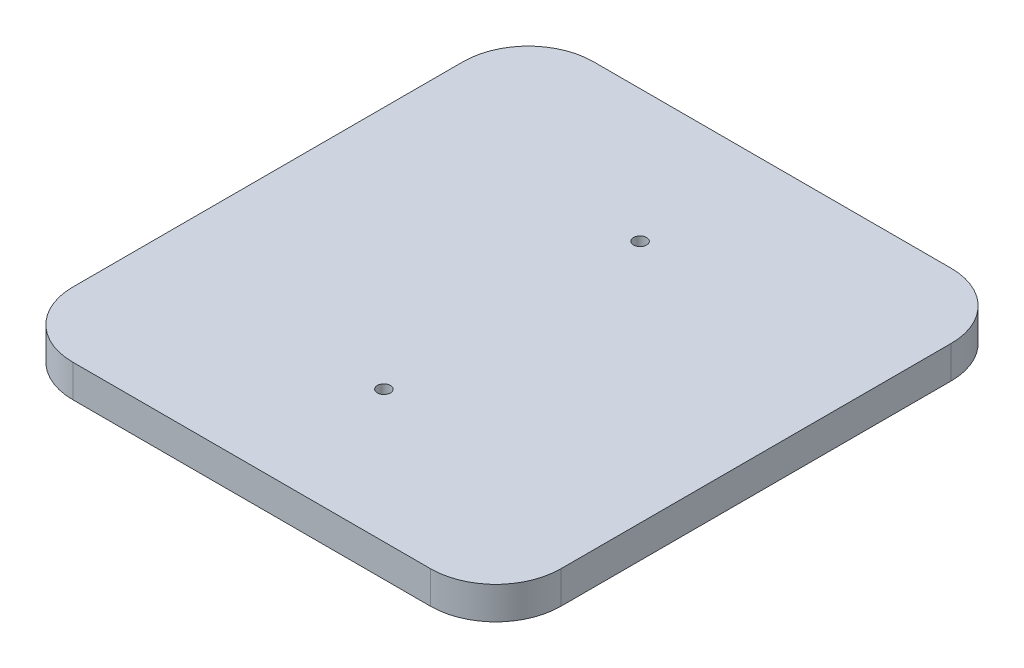
SolidWorks part; units mm, degrees
ref_plane "Front Plane" through (0, 0, 0) normal (0, 0, 1) x (1, 0, 0)
ref_plane "Top Plane" through (0, 0, 0) normal (0, 1, 0) x (1, 0, 0)
ref_plane "Right Plane" through (0, 0, 0) normal (1, 0, 0) x (0, 0, -1)
sketch "Sketch1" plane through (0, 0, 0) normal (0, 1, 0) x (1, 0, 0)
  line L1 (25.4, 0) -> (165.1, 0)
  line L2 (0, 25.4) -> (0, 177.8)
  line L3 (25.4, 203.2) -> (165.1, 203.2)
  line L4 (190.5, 25.4) -> (190.5, 177.8)
  arc A0 (0, 25.4) -> (25.4, 0) centre (25.4, 25.4) ccw
  arc A1 (165.1, 0) -> (190.5, 25.4) centre (165.1, 25.4) ccw
  arc A2 (190.5, 177.8) -> (165.1, 203.2) centre (165.1, 177.8) ccw
  arc A3 (25.4, 203.2) -> (0, 177.8) centre (25.4, 177.8) ccw
  point P7 (0, 0)
  dimension "D1" = 25.4
extrude "Boss-Extrude1" add sketch "Sketch1" along normal blind 12.7
hole_wizard "1/4-20 Tapped Hole2" positions "Sketch5" profile "Sketch4" tap size "1/4-20" standard "ANSI Inch"
sketch "Sketch5" plane through (0, 12.7, 0) normal (0, 1, 0) x (1, 0, 0)
  line L0 (25.4, 0) -> (165.1, 0) construction
  line L1 (0, 177.8) -> (0, 25.4) construction
  point P0 (95.25, 151.6)
  point P2 (95.25, 51.6)
  dimension "D1" = 100
  dimension "D2" = 51.6
  dimension "D3" = 95.25
sketch "Sketch4" plane through (95.25, 12.7, -151.6) normal (1, 0, 0) x (0, 0, 1)
  line L0 (0, 0) -> (0, 20.5838)
  line L1 (0, 20.5838) -> (2.5527, 19.05)
  line L2 (2.5527, 19.05) -> (2.5527, 0)
  line L5 (2.5527, 0) -> (0, 0)
  line L10 (0, 20.5838) -> (-2.5527, 19.05) construction
  line L11 (0, -6.35) -> (0, 107.95) construction
  dimension "Tap Drill Dia." = 5.1054
  dimension "Tap Drill Depth" = 19.05
  dimension "Drill Angle" = 118
cosmetic thread "Hole Thread2" parameters "D1"=12.7, "D2"=6.35
cosmetic thread "Hole Thread3" parameters "D1"=12.7, "D2"=6.35
